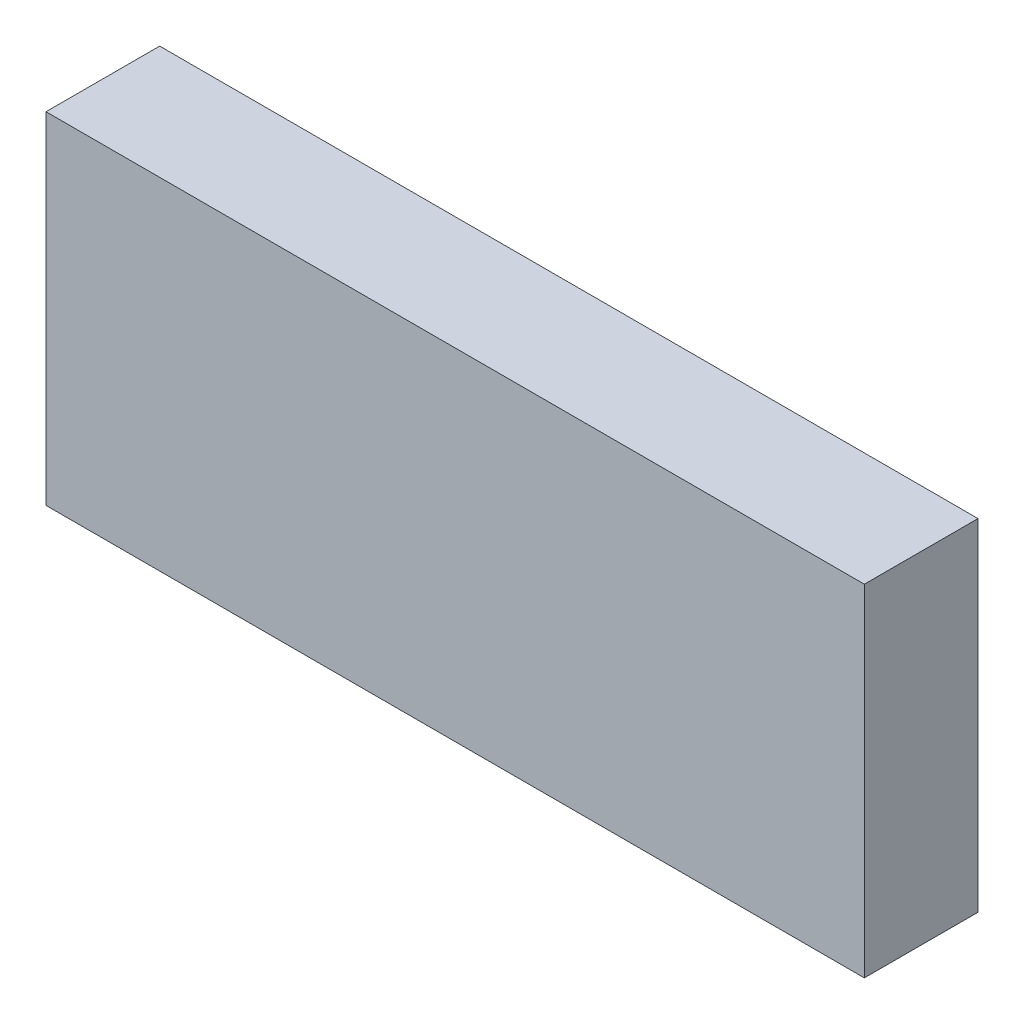
SolidWorks part; units mm, degrees
ref_plane "Front Plane" through (0, 0, 0) normal (0, 0, 1) x (1, 0, 0)
ref_plane "Top Plane" through (0, 0, 0) normal (0, 1, 0) x (1, 0, 0)
ref_plane "Right Plane" through (0, 0, 0) normal (1, 0, 0) x (0, 0, -1)
sketch "Sketch1" plane through (0, 0, 0) normal (0, 0, 1) x (1, 0, 0)
  line L1 (0, 0) -> (228.6, 0)
  line L2 (0, 0) -> (0, 95.25)
  line L3 (0, 95.25) -> (228.6, 95.25)
  line L4 (228.6, 0) -> (228.6, 95.25)
  dimension "D1" = 228.6
  dimension "D2" = 95.25
extrude "Boss-Extrude1" add sketch "Sketch1" along normal blind 31.75
